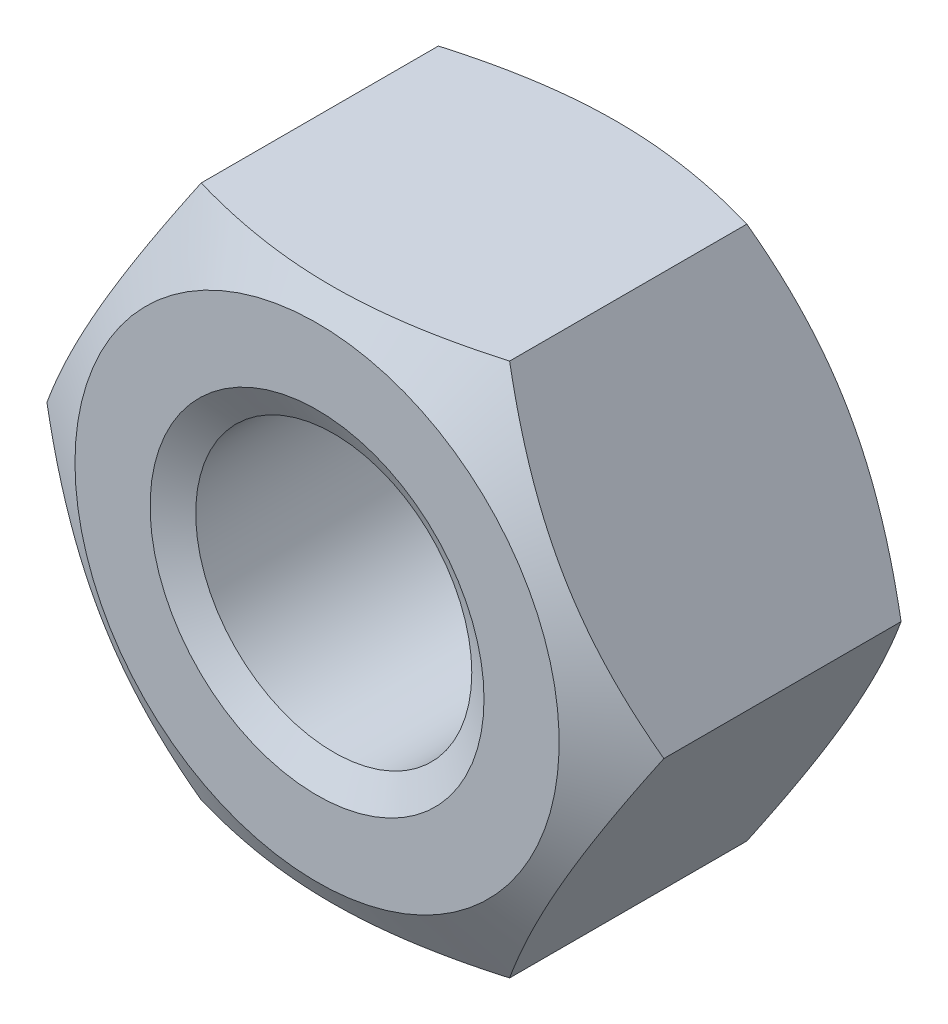
SolidWorks part; units mm, degrees
ref_plane "Front" through (0, 0, 0) normal (0, 0, 1) x (1, 0, 0)
ref_plane "Top" through (0, 0, 0) normal (0, 1, 0) x (1, 0, 0)
ref_plane "Right" through (0, 0, 0) normal (1, 0, 0) x (0, 0, -1)
sketch "Sketch1" plane through (0, 0, 0) normal (0, 0, 1) x (1, 0, 0)
  line L1 (4.6188, 0) -> (2.3094, 4)
  line L2 (2.3094, 4) -> (-2.3094, 4)
  line L3 (-2.3094, 4) -> (-4.6188, 0)
  line L4 (-4.6188, 0) -> (-2.3094, -4)
  line L5 (-2.3094, -4) -> (2.3094, -4)
  line L6 (2.3094, -4) -> (4.6188, 0)
  circle A0 centre (0, 0) radius 4 construction
  circle A1 centre (0, 0) radius 2.067
  dimension "D" = 4.134
  dimension "s" = 8
extrude "BaseNut" add sketch "Sketch1" against normal blind 4.7
cosmetic thread "ThreadCosmetic1" [suppressed] parameters "D"=5
sketch "Sketch2" plane through (0, 0, 0) normal (0, 1, 0) x (1, 0, 0)
  line L0 (-4.6188, 4.7) -> (-3.625, 4.7)
  line L2 (-3.625, 4.7) -> (-4.6188, 4.1262)
  line L3 (-4.6188, 4.1262) -> (-4.6188, 4.7)
  line L4 (0, 3.3759) -> (0, -9.8171) construction
  line L6 (-9.7712, 2.35) -> (9.8853, 2.35) construction
  line L7 (-4.6188, 0.5738) -> (-4.6188, 0)
  line L8 (-3.625, 0) -> (-4.6188, 0.5738)
  line L9 (-4.6188, 0) -> (-3.625, 0)
  dimension "D1" = 30
  dimension "dw" = 7.25
  dimension "D2" = 2.35
revolve "Double-Chamfer" cut sketch "Sketch2" angle 360 about L4
chamfer "EndChamfer" distance 0.433 angle 30 2 edges at (2.067, 0, -4.7) (2.067, 0, 0)
sketch "Sketch3" plane through (0, 0, 0) normal (0, 1, 0) x (1, 0, 0)
  line L0 (-2.442, 4.267) -> (-2.067, 4.0505)
  line L1 (-2.067, 4.0505) -> (-1.634, 4.0505)
  line L2 (-1.634, 4.0505) -> (-1.634, 4.4835)
  line L3 (-1.634, 4.4835) -> (-2.067, 4.4835)
  line L4 (-2.067, 4.4835) -> (-2.442, 4.267)
  line L5 (0, 7.4383) -> (0, 16.8806) construction
  dimension "D1" = 0.433
  dimension "D2" = 4.134
revolve "Cut-Revolve10" [suppressed] cut sketch "Sketch3" angle 360 about L5
pattern_linear "LPattern10" [suppressed] count 9 spacing 0.5196 along (0, 0, -1)
equation "\"dw@Sketch2\" = \"s@Sketch1\"-0.75"
equation "\"D2@Sketch2\" = \"m@BaseNut\" / 2"
equation "\"D2@Sketch3\" = \"D@Sketch1\""
equation "\"D1@Sketch3\" =  (\"D@ThreadCosmetic1\"   - \"D@Sketch1\")  / 2"
equation "\"D3@LPattern10\" = \"D1@Sketch3\" * 1.2"
equation "\"D1@LPattern10\" = \"m@BaseNut\"/\"D3@LPattern10\""
